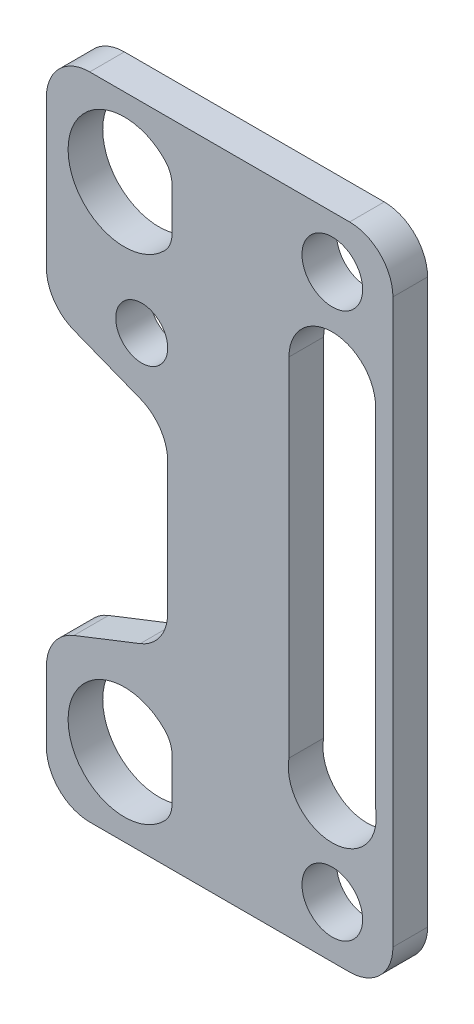
SolidWorks part; units mm, degrees
ref_plane "Plan de face" through (0, 0, 0) normal (0, 0, 1) x (1, 0, 0)
ref_plane "Plan de dessus" through (0, 0, 0) normal (0, 1, 0) x (1, 0, 0)
ref_plane "Plan de droite" through (0, 0, 0) normal (1, 0, 0) x (0, 0, -1)
sketch "Esquisse1" plane through (0, 0, 0) normal (0, 0, 1) x (1, 0, 0)
  line L1 (0, 0) -> (40, 0)
  line L2 (0, 0) -> (0, 75)
  line L3 (0, 75) -> (40, 75)
  line L4 (40, 0) -> (40, 75)
  dimension "D1" = 40
  dimension "D2" = 75
extrude "Boss.-Extru.1" add sketch "Esquisse1" along normal blind 4
sketch "Esquisse2" plane through (0, 0, 4) normal (0, 0, 1) x (1, 0, 0)
  line L0 (0, 16.5) -> (0, 49.5)
  line L1 (0, 75) -> (0, 0) construction
  line L2 (14, 44) -> (14, 22)
  line L3 (0, 33) -> (40, 33) construction
  line L4 (40, 0) -> (40, 75) construction
  line L5 (40, 75) -> (0, 75) construction
  line L6 (0, 49.5) -> (14, 44)
  line L7 (0, 16.5) -> (14, 22)
  point P12 (14, 33)
  dimension "D1" = 42
  dimension "D2" = 22
  dimension "D3" = 33
  dimension "D4" = 14
extrude "Enlèv. mat.-Extru.1" cut sketch "Esquisse2" against normal through all contours L6 L2 L7 L0
sketch "Esquisse3" plane through (0, 0, 4) normal (0, 0, 1) x (1, 0, 0)
  line L0 (9, 66) -> (9, 9) construction
  line L1 (40, 75) -> (0, 75) construction
  line L2 (0, 0) -> (40, 0) construction
  line L3 (0, 16.5) -> (0, 0) construction
  line L4 (11, 51.8905) -> (9, 51.8905) construction
  circle A0 centre (9, 66) radius 6.5
  circle A1 centre (9, 9) radius 6.5
  circle A2 centre (11, 51.8905) radius 3
  dimension "D1" = 13
  dimension "D5" = 6
  dimension "D2" = 9
  dimension "D3" = 9
  dimension "D4" = 9
  dimension "D6" = 4
extrude "Enlèv. mat.-Extru.2" cut sketch "Esquisse3" against normal through all contours A1 | A2 | A0
fillet "Congé1" radius 5 8 edges at (40, 0, 2) (40, 75, 2) (0, 75, 2) (0, 0, 2) (0, 16.5, 2) (14, 22, 2) (14, 44, 2) (0, 49.5, 2)
sketch "Esquisse4" plane through (0, 0, 4) normal (0, 0, 1) x (1, 0, 0)
  line L0 (33, 75) -> (33, 0) construction
  line L1 (35, 75) -> (5, 75) construction
  line L2 (5, 0) -> (35, 0) construction
  line L3 (40, 5) -> (40, 70) construction
  circle A0 centre (33, 69) radius 3.5
  circle A1 centre (33, 6) radius 3.5
  point P12 (0, 0)
  point P13 (0, 0)
  point P14 (28.3192, 0)
  dimension "D2" = 7
  dimension "D1" = 7
  dimension "D3" = 63
  dimension "D4" = 6
extrude "Enlèv. mat.-Extru.3" cut sketch "Esquisse4" against normal through all
sketch "Esquisse5" plane through (0, 0, 4) normal (0, 0, 1) x (1, 0, 0)
  line L0 (33, 69) -> (33, 6) construction
  line L1 (28, 58) -> (28, 17.9014)
  line L2 (33, 58) -> (33, 17) construction
  line L3 (38, 17.9014) -> (38, 58)
  arc A0 (28, 58) -> (38, 58) centre (33, 58) cw
  arc A1 (28, 17.9014) -> (38, 17.9014) centre (33, 17) ccw
  circle A2 centre (33, 69) radius 3.5 construction
  point P10 (0, 0)
  point P11 (0, 0)
  point P12 (0, 0)
  point P13 (33, 56.0518)
  point P14 (33, 17.118)
  point P15 (33, 60.045)
  point P16 (33, 57.2165)
  dimension "D1" = 10
  dimension "D2" = 11
  dimension "D3" = 11
extrude "Enlèv. mat.-Extru.4" cut sketch "Esquisse5" against normal through all both and the other way through all
sketch "Esquisse6" plane through (0, 0, 4) normal (0, 0, 1) x (1, 0, 0)
  line L1 (14.5, 71.6919) -> (18.3268, 71.6919)
  line L2 (14.5, 71.6919) -> (14.5, 58.3812)
  line L3 (14.5, 58.3812) -> (18.3268, 58.3812)
  line L4 (18.3268, 71.6919) -> (18.3268, 58.3812)
  line L5 (14.5, 16.4524) -> (18.3268, 16.4524)
  line L6 (14.5, 16.4524) -> (14.5, 2.3098)
  line L7 (14.5, 2.3098) -> (18.3268, 2.3098)
  line L8 (18.3268, 16.4524) -> (18.3268, 2.3098)
  circle A0 centre (9, 66) radius 6.5 construction
  circle A1 centre (9, 9) radius 6.5 construction
  dimension "D1" = 5.5
  dimension "D2" = 5.5
extrude "Boss.-Extru.2" add sketch "Esquisse6" against normal up to surface (4 mm away) up to face at (33, 37.7052, 0)
fillet "Congé2" radius 3 4 edges at (14.5, 5.5359, 2) (14.5, 12.4641, 2) (14.5, 62.5359, 2) (14.5, 69.4641, 2)
